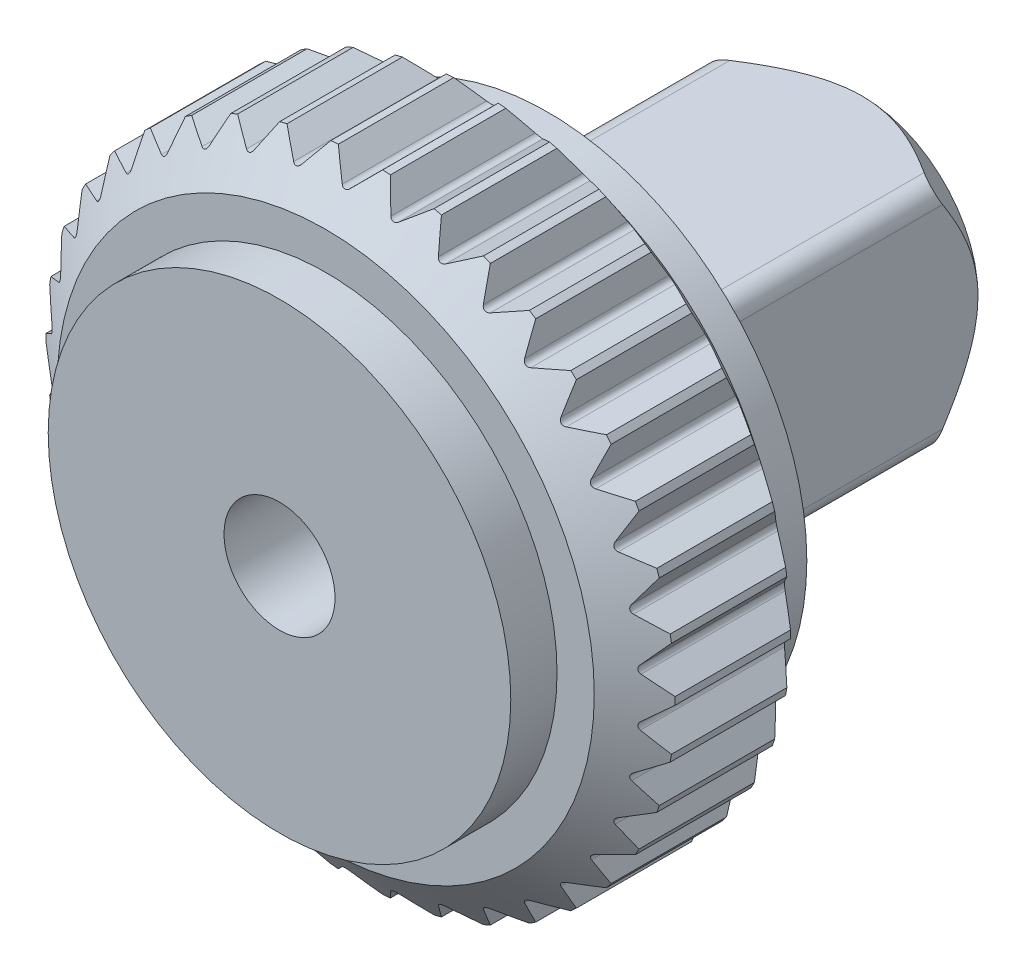
SolidWorks part; units mm, degrees
ref_plane "Front Plane" through (0, 0, 0) normal (0, 0, 1) x (1, 0, 0)
ref_plane "Top Plane" through (0, 0, 0) normal (0, 1, 0) x (1, 0, 0)
ref_plane "Right Plane" through (0, 0, 0) normal (1, 0, 0) x (0, 0, -1)
sketch "Szkic1" plane through (0, 0, 0) normal (0, 0, 1) x (1, 0, 0)
  line L0 (0, 0) -> (0, 17) construction
  line L1 (0.2121, 15.9697) -> (1.2, 16.9576)
  line L2 (-0.2121, 15.9697) -> (-1.2, 16.9576)
  line L3 (2.4193, 15.7868) -> (1.6075, 16.9238)
  line L4 (2.8378, 15.717) -> (3.9748, 16.5288)
  line L5 (4.9847, 15.1733) -> (4.3711, 16.4284)
  line L6 (5.386, 15.0356) -> (6.6411, 15.6491)
  line L7 (7.4142, 14.1459) -> (7.0156, 15.4849)
  line L8 (7.7873, 13.944) -> (9.1263, 14.3426)
  line L9 (9.6414, 12.7327) -> (9.4686, 14.119)
  line L10 (9.9762, 12.4721) -> (11.3625, 12.6449)
  line L11 (11.6056, 10.9721) -> (11.6634, 12.3679)
  line L12 (11.893, 10.6599) -> (13.2888, 10.6022)
  line L13 (13.2533, 8.9122) -> (13.54, 10.2795)
  line L14 (13.4853, 8.557) -> (14.8527, 8.2703)
  line L15 (14.5394, 6.6092) -> (15.0473, 7.9107)
  line L16 (14.7099, 6.2207) -> (16.0113, 5.7129)
  line L17 (15.429, 4.126) -> (16.1441, 5.3261)
  line L18 (15.5331, 3.7147) -> (16.7333, 2.9996)
  line L19 (15.8977, 1.5302) -> (16.8006, 2.5962)
  line L20 (15.9327, 1.1074) -> (16.9988, 0.2044)
  line L21 (15.9327, -1.1074) -> (16.9988, -0.2044)
  line L22 (15.8977, -1.5302) -> (16.8006, -2.5962)
  line L23 (15.5331, -3.7147) -> (16.7333, -2.9996)
  line L24 (15.429, -4.126) -> (16.1441, -5.3261)
  line L25 (14.7099, -6.2207) -> (16.0113, -5.7129)
  line L26 (14.5394, -6.6092) -> (15.0473, -7.9107)
  line L27 (13.4853, -8.557) -> (14.8527, -8.2703)
  line L28 (13.2533, -8.9122) -> (13.54, -10.2795)
  line L29 (11.893, -10.6599) -> (13.2888, -10.6022)
  line L30 (11.6056, -10.9721) -> (11.6634, -12.3679)
  line L31 (9.9762, -12.4721) -> (11.3625, -12.6449)
  line L32 (9.6414, -12.7327) -> (9.4686, -14.119)
  line L33 (7.7873, -13.944) -> (9.1263, -14.3426)
  line L34 (7.4142, -14.1459) -> (7.0156, -15.4849)
  line L35 (5.386, -15.0356) -> (6.6411, -15.6491)
  line L36 (4.9847, -15.1733) -> (4.3711, -16.4284)
  line L37 (2.8378, -15.717) -> (3.9748, -16.5288)
  line L38 (2.4193, -15.7868) -> (1.6075, -16.9238)
  line L39 (0.2121, -15.9697) -> (1.2, -16.9576)
  line L40 (-0.2121, -15.9697) -> (-1.2, -16.9576)
  line L41 (-2.4193, -15.7868) -> (-1.6075, -16.9238)
  line L42 (-2.8378, -15.717) -> (-3.9748, -16.5288)
  line L43 (-4.9847, -15.1733) -> (-4.3711, -16.4284)
  line L44 (-5.386, -15.0356) -> (-6.6411, -15.6491)
  line L45 (-7.4142, -14.1459) -> (-7.0156, -15.4849)
  line L46 (-7.7873, -13.944) -> (-9.1263, -14.3426)
  line L47 (-9.6414, -12.7327) -> (-9.4686, -14.119)
  line L48 (-9.9762, -12.4721) -> (-11.3625, -12.6449)
  line L49 (-11.6056, -10.9721) -> (-11.6634, -12.3679)
  line L50 (-11.893, -10.6599) -> (-13.2888, -10.6022)
  line L51 (-13.2533, -8.9122) -> (-13.54, -10.2795)
  line L52 (-13.4853, -8.557) -> (-14.8527, -8.2703)
  line L53 (-14.5394, -6.6092) -> (-15.0473, -7.9107)
  line L54 (-14.7099, -6.2207) -> (-16.0113, -5.7129)
  line L55 (-15.429, -4.126) -> (-16.1441, -5.3261)
  line L56 (-15.5331, -3.7147) -> (-16.7333, -2.9996)
  line L57 (-15.8977, -1.5302) -> (-16.8006, -2.5962)
  line L58 (-15.9327, -1.1074) -> (-16.9988, -0.2044)
  line L59 (-15.9327, 1.1074) -> (-16.9988, 0.2044)
  line L60 (-15.8977, 1.5302) -> (-16.8006, 2.5962)
  line L61 (-15.5331, 3.7147) -> (-16.7333, 2.9996)
  line L62 (-15.429, 4.126) -> (-16.1441, 5.3261)
  line L63 (-14.7099, 6.2207) -> (-16.0113, 5.7129)
  line L64 (-14.5394, 6.6092) -> (-15.0473, 7.9107)
  line L65 (-13.4853, 8.557) -> (-14.8527, 8.2703)
  line L66 (-13.2533, 8.9122) -> (-13.54, 10.2795)
  line L67 (-11.893, 10.6599) -> (-13.2888, 10.6022)
  line L68 (-11.6056, 10.9721) -> (-11.6634, 12.3679)
  line L69 (-9.9762, 12.4721) -> (-11.3625, 12.6449)
  line L70 (-9.6414, 12.7327) -> (-9.4686, 14.119)
  line L71 (-7.7873, 13.944) -> (-9.1263, 14.3426)
  line L72 (-7.4142, 14.1459) -> (-7.0156, 15.4849)
  line L73 (-5.386, 15.0356) -> (-6.6411, 15.6491)
  line L74 (-4.9847, 15.1733) -> (-4.3711, 16.4284)
  line L75 (-2.8378, 15.717) -> (-3.9748, 16.5288)
  line L76 (-2.4193, 15.7868) -> (-1.6075, 16.9238)
  arc A0 (-3.9748, 16.5288) -> (-4.3711, 16.4284) centre (0, 0) ccw
  arc A1 (0.2121, 15.9697) -> (-0.2121, 15.9697) centre (0, 16.1819) cw
  arc A2 (2.8378, 15.717) -> (2.4193, 15.7868) centre (2.6634, 15.9612) cw
  arc A3 (5.386, 15.0356) -> (4.9847, 15.1733) centre (5.2542, 15.3051) cw
  arc A4 (7.7873, 13.944) -> (7.4142, 14.1459) centre (7.7017, 14.2315) cw
  arc A5 (9.9762, 12.4721) -> (9.6414, 12.7327) centre (9.9391, 12.7698) cw
  arc A6 (11.893, 10.6599) -> (11.6056, 10.9721) centre (11.9054, 10.9597) cw
  arc A7 (13.4853, 8.557) -> (13.2533, 8.9122) centre (13.5469, 8.8506) cw
  arc A8 (14.7099, 6.2207) -> (14.5394, 6.6092) centre (14.8189, 6.5002) cw
  arc A9 (15.5331, 3.7147) -> (15.429, 4.126) centre (15.6867, 3.9724) cw
  arc A10 (15.9327, 1.1074) -> (15.8977, 1.5302) centre (16.1266, 1.3363) cw
  arc A11 (15.8977, -1.5302) -> (15.9327, -1.1074) centre (16.1266, -1.3363) cw
  arc A12 (15.429, -4.126) -> (15.5331, -3.7147) centre (15.6867, -3.9724) cw
  arc A13 (14.5394, -6.6092) -> (14.7099, -6.2207) centre (14.8189, -6.5002) cw
  arc A14 (13.2533, -8.9122) -> (13.4853, -8.557) centre (13.5469, -8.8506) cw
  arc A15 (11.6056, -10.9721) -> (11.893, -10.6599) centre (11.9054, -10.9597) cw
  arc A16 (9.6414, -12.7327) -> (9.9762, -12.4721) centre (9.9391, -12.7698) cw
  arc A17 (7.4142, -14.1459) -> (7.7873, -13.944) centre (7.7017, -14.2315) cw
  arc A18 (4.9847, -15.1733) -> (5.386, -15.0356) centre (5.2542, -15.3051) cw
  arc A19 (2.4193, -15.7868) -> (2.8378, -15.717) centre (2.6634, -15.9612) cw
  arc A20 (-0.2121, -15.9697) -> (0.2121, -15.9697) centre (0, -16.1819) cw
  arc A21 (-2.8378, -15.717) -> (-2.4193, -15.7868) centre (-2.6634, -15.9612) cw
  arc A22 (-5.386, -15.0356) -> (-4.9847, -15.1733) centre (-5.2542, -15.3051) cw
  arc A23 (-7.7873, -13.944) -> (-7.4142, -14.1459) centre (-7.7017, -14.2315) cw
  arc A24 (-9.9762, -12.4721) -> (-9.6414, -12.7327) centre (-9.9391, -12.7698) cw
  arc A25 (-11.893, -10.6599) -> (-11.6056, -10.9721) centre (-11.9054, -10.9597) cw
  arc A26 (-13.4853, -8.557) -> (-13.2533, -8.9122) centre (-13.5469, -8.8506) cw
  arc A27 (-14.7099, -6.2207) -> (-14.5394, -6.6092) centre (-14.8189, -6.5002) cw
  arc A28 (-15.5331, -3.7147) -> (-15.429, -4.126) centre (-15.6867, -3.9724) cw
  arc A29 (-15.9327, -1.1074) -> (-15.8977, -1.5302) centre (-16.1266, -1.3363) cw
  arc A30 (-15.8977, 1.5302) -> (-15.9327, 1.1074) centre (-16.1266, 1.3363) cw
  arc A31 (-15.429, 4.126) -> (-15.5331, 3.7147) centre (-15.6867, 3.9724) cw
  arc A32 (-14.5394, 6.6092) -> (-14.7099, 6.2207) centre (-14.8189, 6.5002) cw
  arc A33 (-13.2533, 8.9122) -> (-13.4853, 8.557) centre (-13.5469, 8.8506) cw
  arc A34 (-11.6056, 10.9721) -> (-11.893, 10.6599) centre (-11.9054, 10.9597) cw
  arc A35 (-9.6414, 12.7327) -> (-9.9762, 12.4721) centre (-9.9391, 12.7698) cw
  arc A36 (-7.4142, 14.1459) -> (-7.7873, 13.944) centre (-7.7017, 14.2315) cw
  arc A37 (-4.9847, 15.1733) -> (-5.386, 15.0356) centre (-5.2542, 15.3051) cw
  arc A38 (-2.4193, 15.7868) -> (-2.8378, 15.717) centre (-2.6634, 15.9612) cw
  arc A39 (-6.6411, 15.6491) -> (-7.0156, 15.4849) centre (0, 0) ccw
  arc A40 (-9.1263, 14.3426) -> (-9.4686, 14.119) centre (0, 0) ccw
  arc A41 (-11.3625, 12.6449) -> (-11.6634, 12.3679) centre (0, 0) ccw
  arc A42 (-1.2, 16.9576) -> (-1.6075, 16.9238) centre (0, 0) ccw
  arc A43 (1.6075, 16.9238) -> (1.2, 16.9576) centre (0, 0) ccw
  arc A44 (4.3711, 16.4284) -> (3.9748, 16.5288) centre (0, 0) ccw
  arc A45 (-13.2888, 10.6022) -> (-13.54, 10.2795) centre (0, 0) ccw
  arc A46 (-14.8527, 8.2703) -> (-15.0473, 7.9107) centre (0, 0) ccw
  arc A47 (-16.0113, 5.7129) -> (-16.1441, 5.3261) centre (0, 0) ccw
  arc A48 (-16.7333, 2.9996) -> (-16.8006, 2.5962) centre (0, 0) ccw
  arc A49 (-16.9988, 0.2044) -> (-16.9988, -0.2044) centre (0, 0) ccw
  arc A50 (-16.8006, -2.5962) -> (-16.7333, -2.9996) centre (0, 0) ccw
  arc A51 (-16.1441, -5.3261) -> (-16.0113, -5.7129) centre (0, 0) ccw
  arc A52 (-15.0473, -7.9107) -> (-14.8527, -8.2703) centre (0, 0) ccw
  arc A53 (-13.54, -10.2795) -> (-13.2888, -10.6022) centre (0, 0) ccw
  arc A54 (-11.6634, -12.3679) -> (-11.3625, -12.6449) centre (0, 0) ccw
  arc A55 (-9.4686, -14.119) -> (-9.1263, -14.3426) centre (0, 0) ccw
  arc A56 (-7.0156, -15.4849) -> (-6.6411, -15.6491) centre (0, 0) ccw
  arc A57 (-4.3711, -16.4284) -> (-3.9748, -16.5288) centre (0, 0) ccw
  arc A58 (-1.6075, -16.9238) -> (-1.2, -16.9576) centre (0, 0) ccw
  arc A59 (1.2, -16.9576) -> (1.6075, -16.9238) centre (0, 0) ccw
  arc A60 (3.9748, -16.5288) -> (4.3711, -16.4284) centre (0, 0) ccw
  arc A61 (6.6411, -15.6491) -> (7.0156, -15.4849) centre (0, 0) ccw
  arc A62 (9.1263, -14.3426) -> (9.4686, -14.119) centre (0, 0) ccw
  arc A63 (11.3625, -12.6449) -> (11.6634, -12.3679) centre (0, 0) ccw
  arc A64 (13.2888, -10.6022) -> (13.54, -10.2795) centre (0, 0) ccw
  arc A65 (14.8527, -8.2703) -> (15.0473, -7.9107) centre (0, 0) ccw
  arc A66 (16.0113, -5.7129) -> (16.1441, -5.3261) centre (0, 0) ccw
  arc A67 (16.7333, -2.9996) -> (16.8006, -2.5962) centre (0, 0) ccw
  arc A68 (16.9988, -0.2044) -> (16.9988, 0.2044) centre (0, 0) ccw
  arc A69 (16.8006, 2.5962) -> (16.7333, 2.9996) centre (0, 0) ccw
  arc A70 (16.1441, 5.3261) -> (16.0113, 5.7129) centre (0, 0) ccw
  arc A71 (15.0473, 7.9107) -> (14.8527, 8.2703) centre (0, 0) ccw
  arc A72 (13.54, 10.2795) -> (13.2888, 10.6022) centre (0, 0) ccw
  arc A73 (11.6634, 12.3679) -> (11.3625, 12.6449) centre (0, 0) ccw
  arc A74 (9.4686, 14.119) -> (9.1263, 14.3426) centre (0, 0) ccw
  arc A75 (7.0156, 15.4849) -> (6.6411, 15.6491) centre (0, 0) ccw
  point P9 (0, 15.7576)
  point P198 (0, 0)
  dimension "D1" = 34
  dimension "D4" = 0.3
  dimension "D2" = 45
  dimension "D3" = 1.2
  dimension "D5" = 38
extrude "Dodanie-wyciągnięcie1" add sketch "Szkic1" along normal blind 10
sketch "Szkic2" plane through (0, 0, 0) normal (1, 0, 0) x (0, 0, -1)
  line L0 (-5, 16.9238) -> (-5, -16.9576) construction
  line L1 (-10, 16.9238) -> (0, 16.9238) construction
  line L2 (-10, -16.9576) -> (0, -16.9576) construction
  line L3 (-10, 14.5114) -> (-10, 17.1576)
  line L4 (-10, 14.1459) -> (-10, 15.4849) construction
  line L5 (-10, 17.1576) -> (-8, 17.1576)
  line L6 (-8, 17.1576) -> (-10, 14.5114)
  line L7 (-10, 16.9576) -> (0, 16.9576) construction
  line L8 (-2, 17.1576) -> (0, 14.5114)
  line L9 (0, 14.5114) -> (0, 17.1576)
  line L10 (0, 17.1576) -> (-2, 17.1576)
  dimension "D1" = 2.4124
  dimension "D2" = 0.2
  dimension "D3" = 2
revolve "Wycięcie-obrót1" cut sketch "Szkic2" angle 360 about axis through (0, 0, 10) along (0, 0, -1)
sketch "Szkic3" plane through (0, 0, 10) normal (0, 0, 1) x (1, 0, 0)
  circle A0 centre (0, 0) radius 12.5
  dimension "D1" = 25
extrude "Dodanie-wyciągnięcie2" add sketch "Szkic3" along normal blind 2.5
sketch "Szkic4" plane through (0, 0, 0) normal (0, 0, -1) x (-1, 0, 0)
  circle A0 centre (0, 0) radius 14
  dimension "D1" = 28
extrude "Dodanie-wyciągnięcie3" add sketch "Szkic4" along normal blind 2
sketch "Szkic5" plane through (0, 0, -2) normal (0, 0, -1) x (-1, 0, 0)
  line L1 (-5.25, -6.25) -> (5.25, -6.25)
  line L2 (-6.25, -5.25) -> (-6.25, 5.25)
  line L3 (-5.25, 6.25) -> (5.25, 6.25)
  line L4 (6.25, -5.25) -> (6.25, 5.25)
  line L5 (-6.25, -6.25) -> (6.25, 6.25) construction
  line L6 (-6.25, 6.25) -> (6.25, -6.25) construction
  arc A0 (5.25, 6.25) -> (6.25, 5.25) centre (5.25, 5.25) cw
  arc A1 (5.25, -6.25) -> (6.25, -5.25) centre (5.25, -5.25) ccw
  arc A2 (-5.25, -6.25) -> (-6.25, -5.25) centre (-5.25, -5.25) cw
  arc A3 (-6.25, 5.25) -> (-5.25, 6.25) centre (-5.25, 5.25) cw
  point P0 (0, 0)
  dimension "D3" = 1
  dimension "D1" = 12.5
extrude "Dodanie-wyciągnięcie4" add sketch "Szkic5" along normal blind 17
fillet "Zaokrąglenie1" radius 1 8 edges at (5.9571, 5.9571, -2) (0, 6.25, -2) (-5.9571, 5.9571, -2) (-6.25, 0, -2) (-5.9571, -5.9571, -2) (0, -6.25, -2) (5.9571, -5.9571, -2) (6.25, 0, -2)
sketch "Szkic6" plane through (0, 0, -19) normal (0, 0, -1) x (-1, 0, 0)
  circle A0 centre (0, 0) radius 3
  dimension "D1" = 6
extrude "Wytnij-wyciągnięcie1" cut sketch "Szkic6" against normal through all
sketch "Szkic7" plane through (0, 0, -19) normal (0, 0, -1) x (-1, 0, 0)
  circle A0 centre (0, 0) radius 6.25
  dimension "D1" = 12.5
extrude "Wytnij-wyciągnięcie2" cut sketch "Szkic7" against normal blind 17 draft 45 flip side to cut
equation "\"Zlaczka1\"=12.5"
